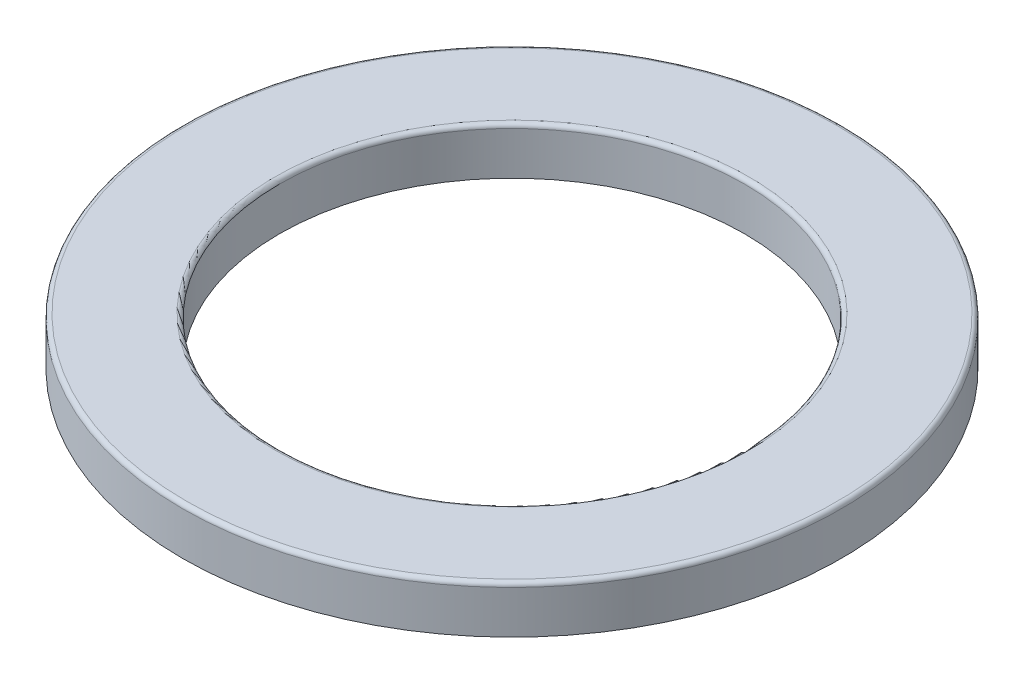
SolidWorks part; units mm, degrees
ref_plane "Front Plane" through (0, 0, 0) normal (0, 0, 1) x (1, 0, 0)
ref_plane "Top Plane" through (0, 0, 0) normal (0, 1, 0) x (1, 0, 0)
ref_plane "Right Plane" through (0, 0, 0) normal (1, 0, 0) x (0, 0, -1)
sketch "Sketch1" plane through (0, 0, 0) normal (0, 1, 0) x (1, 0, 0)
  circle A0 centre (0, 0) radius 85
  circle A1 centre (0, 0) radius 60
  dimension "D1" = 170
  dimension "D2" = 120
extrude "Boss-Extrude1" add sketch "Sketch1" along normal blind 12.2
fillet "Fillet1" radius 1.1 2 edges at (0, 12.2, 60) (0, 12.2, 85)
sketch "Sketch2" plane through (0, 0, 0) normal (0, 0, 1) x (1, 0, 0)
  line L0 (-85, 0) -> (85, 0) construction
  line L1 (-77.98, 0) -> (-67.02, 0)
  arc A0 (-77.98, 0) -> (-67.02, 0) centre (-72.5, -7.3025) cw
  dimension "D1" = 9.13
  dimension "D2" = 67.02
  dimension "D3" = 77.98
ref_axis "Axis1" through (0, 11.1, 0) along (0, -1, 0)
revolve "Cut-Revolve1" cut sketch "Sketch2" angle 360 about axis through (0, 11.1, 0) along (0, -1, 0)
